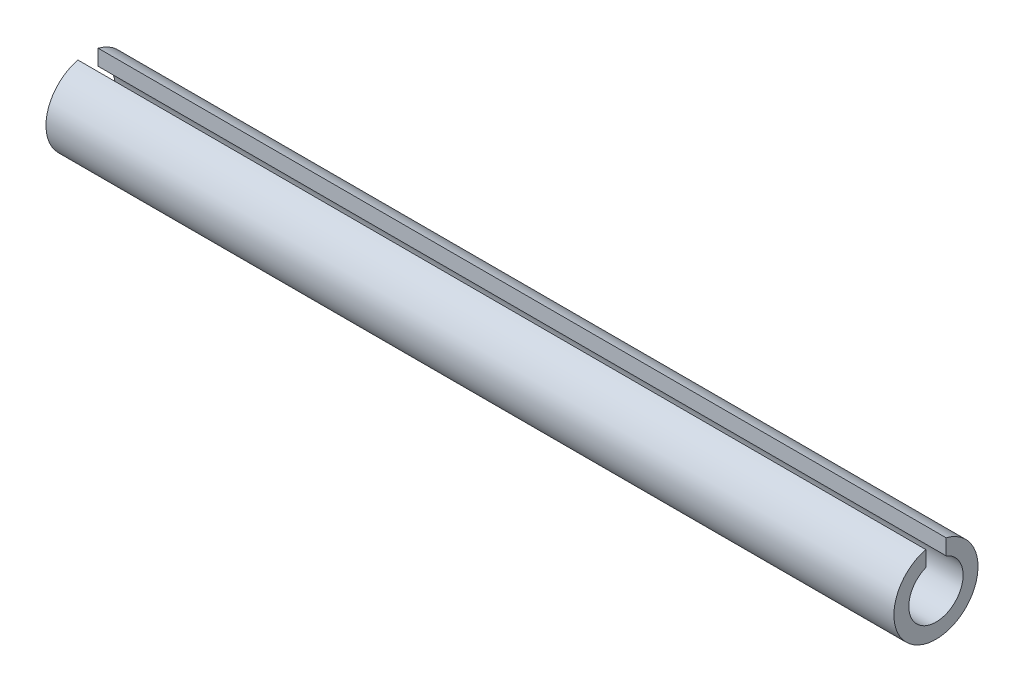
SolidWorks part; units mm, degrees
ref_plane "Front Plane" through (0, 0, 0) normal (0, 0, 1) x (1, 0, 0)
ref_plane "Top Plane" through (0, 0, 0) normal (0, 1, 0) x (1, 0, 0)
ref_plane "Right Plane" through (0, 0, 0) normal (1, 0, 0) x (0, 0, -1)
sketch "Sketch1" plane through (0, 0, 0) normal (1, 0, 0) x (0, 0, -1)
  line L0 (0.1905, 0.4709) -> (0.1905, 0.764)
  line L2 (-0.1905, 0.764) -> (-0.1905, 0.4709)
  arc A0 (-0.1905, 0.764) -> (0.1905, 0.764) centre (0, 0) ccw
  arc A1 (-0.1905, 0.4709) -> (0.1905, 0.4709) centre (0, 0) ccw
  dimension "D1" = 0.381
  dimension "D2" = 0.1905
extrude "Boss-Extrude1" add sketch "Sketch1" along normal blind 15.875
